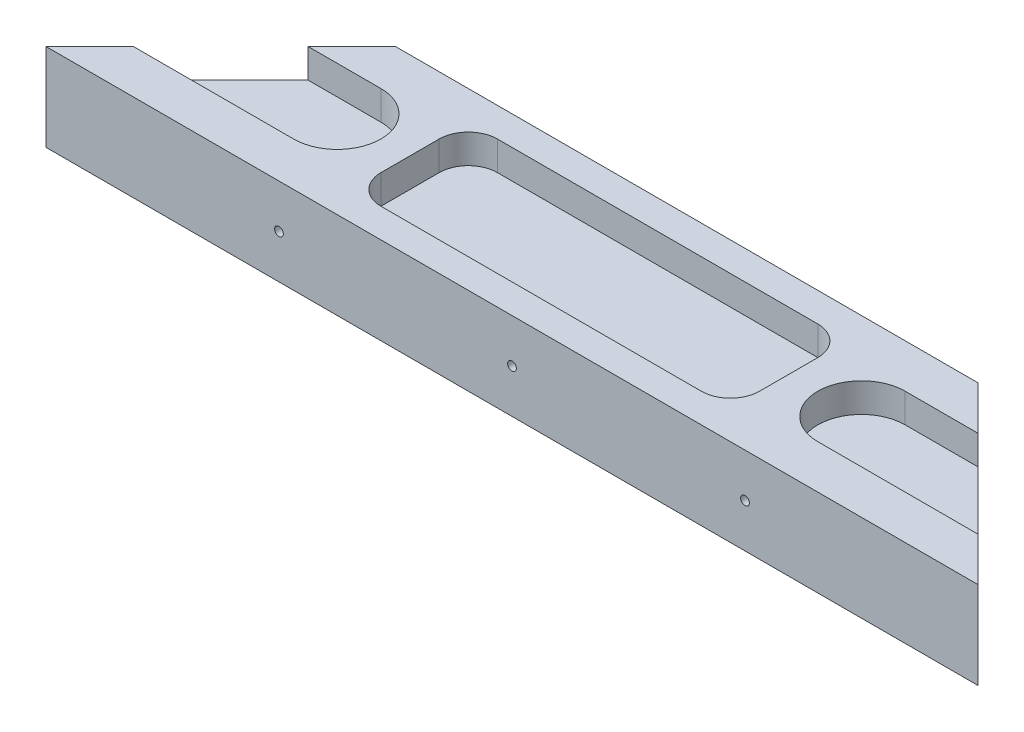
SolidWorks part; units mm, degrees
ref_plane "Front Plane" through (0, 0, 0) normal (0, 0, 1) x (1, 0, 0)
ref_plane "Top Plane" through (0, 0, 0) normal (0, 1, 0) x (1, 0, 0)
ref_plane "Right Plane" through (0, 0, 0) normal (1, 0, 0) x (0, 0, -1)
sketch "Sketch1" plane through (0, 0, 0) normal (0, 1, 0) x (1, 0, 0)
  line L0 (0, 0) -> (160, 0)
  line L1 (160, 0) -> (130, 30)
  line L2 (130, 30) -> (30, 30)
  line L3 (30, 30) -> (0, 0)
  point P3 (80, 30)
  point P6 (80, 0)
  dimension "D1" = 160
  dimension "D2" = 30
  dimension "D3" = 100
extrude "Boss-Extrude1" add sketch "Sketch1" along normal blind 15
sketch "Sketch2" plane through (0, 15, 0) normal (0, 1, 0) x (1, 0, 0)
  line L0 (-5, 15) -> (35, 15) construction
  line L1 (-5, 22.5) -> (35, 22.5)
  line L2 (-5, 7.5) -> (35, 7.5)
  line L3 (30, 30) -> (0, 0) construction
  line L4 (80, 30) -> (80, 0) construction
  line L5 (130, 30) -> (30, 30) construction
  line L6 (0, 0) -> (160, 0) construction
  line L7 (165, 15) -> (125, 15) construction
  line L8 (165, 22.5) -> (125, 22.5)
  line L9 (165, 7.5) -> (125, 7.5)
  arc A0 (-5, 22.5) -> (-5, 7.5) centre (-5, 15) ccw
  arc A1 (35, 7.5) -> (35, 22.5) centre (35, 15) ccw
  arc A2 (165, 22.5) -> (165, 7.5) centre (165, 15) cw
  arc A3 (125, 7.5) -> (125, 22.5) centre (125, 15) cw
  point P2 (15, 15)
  point P9 (15, 15)
  point P18 (145, 15)
  dimension "D1" = 40
  dimension "D2" = 15
extrude "Cut-Extrude1" cut sketch "Sketch2" against normal blind 5
sketch "Sketch3" plane through (0, 0, 0) normal (0, 0, 1) x (1, 0, 0)
  line L0 (0, 7.5) -> (160, 7.5) construction
  line L1 (0, 15) -> (0, 0) construction
  line L2 (160, 15) -> (160, 0) construction
  circle A0 centre (80, 7.5) radius 0.75
  circle A1 centre (40, 7.5) radius 0.75
  circle A2 centre (120, 7.5) radius 0.75
  dimension "D1" = 1.5
  dimension "D2" = 40
  dimension "D3" = 40
extrude "Cut-Extrude2" cut sketch "Sketch3" against normal up to surface (30 mm away) up to face at (80, 7.5, -30)
sketch "Sketch4" plane through (0, 15, 0) normal (0, 1, 0) x (1, 0, 0)
  line L0 (0, 0) -> (160, 0) construction
  line L1 (52.5, 25) -> (107.5, 25)
  line L2 (47.5, 20) -> (47.5, 10)
  line L3 (52.5, 5) -> (107.5, 5)
  line L4 (112.5, 20) -> (112.5, 10)
  line L5 (130, 30) -> (30, 30) construction
  arc A0 (35, 7.5) -> (35, 22.5) centre (35, 15) ccw construction
  arc A1 (125, 22.5) -> (125, 7.5) centre (125, 15) ccw construction
  arc A2 (107.5, 25) -> (112.5, 20) centre (107.5, 20) cw
  arc A3 (107.5, 5) -> (112.5, 10) centre (107.5, 10) ccw
  arc A4 (47.5, 10) -> (52.5, 5) centre (52.5, 10) ccw
  arc A5 (52.5, 25) -> (47.5, 20) centre (52.5, 20) ccw
  point P4 (42.5, 15)
  point P5 (117.5, 15)
  dimension "D5" = 5
  dimension "D1" = 5
  dimension "D2" = 5
  dimension "D3" = 5
  dimension "D4" = 5
extrude "Cut-Extrude3" cut sketch "Sketch4" against normal blind 5
